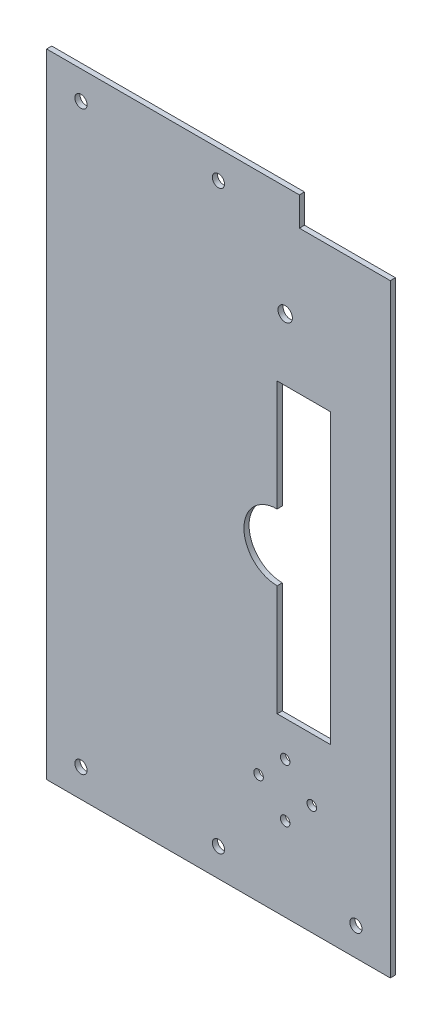
SolidWorks part; units mm, degrees
material "5052-H32"
ref_plane "Front Plane" through (0, 0, 0) normal (0, 0, 1) x (1, 0, 0)
ref_plane "Top Plane" through (0, 0, 0) normal (0, 1, 0) x (1, 0, 0)
ref_plane "Right Plane" through (0, 0, 0) normal (1, 0, 0) x (0, 0, -1)
sketch "Sketch1" plane through (0, 0, 0) normal (0, 0, 1) x (1, 0, 0)
  line L0 (55, 0) -> (-55, 0) construction
  line L1 (-77.5, 142.695) -> (77.5, 142.695)
  line L2 (-77.5, 142.695) -> (-77.5, -142.695)
  line L3 (-77.5, -142.695) -> (77.5, -142.695)
  line L4 (77.5, 142.695) -> (77.5, -142.695)
  line L5 (-77.5, 142.695) -> (77.5, -142.695) construction
  line L6 (-77.5, -142.695) -> (77.5, 142.695) construction
  point P0 (0, 0)
  point P5 (-62, 129.995)
  point P7 (0, 129.995)
  point P8 (62, 129.995)
  point P13 (62, -129.995)
  point P14 (0, -129.995)
  point P15 (-62, -129.995)
  dimension "D1" = 155
  dimension "D2" = 285.39
  dimension "D3" = 15.5
  dimension "D4" = 15.5
  dimension "D5" = 12.7
extrude "Boss-Extrude1" add sketch "Sketch1" along normal blind 2.305
hole_wizard "M5 Clearance Hole1" positions "Sketch2" profile "Sketch3" hole size "M5" standard "ANSI Metric" end condition through all
sketch "Sketch2" plane through (0, 0, 2.305) normal (0, 0, 1) x (1, 0, 0)
  point P0 (-62, 129.995)
  point P3 (0, 129.995)
  point P9 (-62, -129.995)
  point P12 (0, -129.995)
  point P15 (62, -129.995)
  point P19 (0, 0)
sketch "Sketch3" plane through (-62, 129.995, 2.305) normal (1, 0, 0) x (0, -1, 0)
  line L0 (0, 0) -> (0, 2.305)
  line L1 (0, 2.305) -> (2.75, 2.305)
  line L2 (2.75, 2.305) -> (2.75, 0)
  line L5 (2.75, 0) -> (0, 0)
  line L11 (0, -6.35) -> (0, 107.95) construction
  dimension "Thru Hole Dia." = 5.5
  dimension "Thru Hole Depth" = 2.305
sketch "Sketch4" plane through (0, 0, 2.305) normal (0, 0, 1) x (1, 0, 0)
  line L0 (18.1, -93) -> (42.1, -93) construction
  line L1 (30.1, -81) -> (30.1, -105) construction
  line L2 (-77.5, -142.695) -> (77.5, -142.695) construction
  line L4 (77.5, -142.695) -> (77.5, 142.695) construction
  line L5 (30.1, -93) -> (30.1, 93) construction
  line L6 (77.5, 142.695) -> (-77.5, 142.695) construction
  circle A0 centre (30.1, -93) radius 16 construction
  circle A1 centre (30.1, -93) radius 12 construction
  circle A2 centre (30.1, -81) radius 2.15
  circle A3 centre (42.1, -93) radius 2.15
  circle A4 centre (30.1, -105) radius 2.15
  circle A5 centre (18.1, -93) radius 2.15
  circle A6 centre (30.1, 93) radius 3.25
  dimension "D1" = 32
  dimension "D2" = 24
  dimension "D3" = 4.3
  dimension "D6" = 6.5
  dimension "D4" = 49.695
  dimension "D5" = 47.4
  dimension "D7" = 49.695
extrude "Cut-Extrude1" cut sketch "Sketch4" against normal through all
sketch "Sketch5" plane through (0, 0, 2.305) normal (0, 0, 1) x (1, 0, 0)
  line L1 (77.5, 142.695) -> (36.5, 142.695)
  line L2 (77.5, 142.695) -> (77.5, 129.695)
  line L3 (77.5, 129.695) -> (36.5, 129.695)
  line L4 (36.5, 142.695) -> (36.5, 129.695)
  line L5 (77.5, 142.695) -> (36.5, 129.695) construction
  line L6 (77.5, 129.695) -> (36.5, 142.695) construction
  point P4 (57, 136.195)
  dimension "D1" = 13
  dimension "D2" = 41
extrude "Cut-Extrude2" cut sketch "Sketch5" against normal blind 10
sketch "Sketch6" plane through (0, 0, 2.305) normal (0, 0, 1) x (1, 0, 0)
  line L0 (77.5, -142.695) -> (77.5, 129.695) construction
  line L1 (26.5, 65) -> (50.5, 65)
  line L2 (26.5, 65) -> (26.5, 15)
  line L3 (26.5, -65) -> (50.5, -65)
  line L4 (50.5, 65) -> (50.5, -65)
  line L5 (26.5, 65) -> (50.5, -65) construction
  line L6 (26.5, -65) -> (50.5, 65) construction
  line L7 (26.5, -15) -> (26.5, -65)
  arc A0 (26.5, 15) -> (26.5, -15) centre (26.5, 0) ccw
  point P4 (38.5, 0)
  dimension "D4" = 30
  dimension "D1" = 130
  dimension "D2" = 24
  dimension "D3" = 27
extrude "Cut-Extrude3" cut sketch "Sketch6" against normal through all
equation "\"D2@Sketch4\"=(32+16)/2"
equation "\"D7@Sketch4\"=\"D4@Sketch4\""
